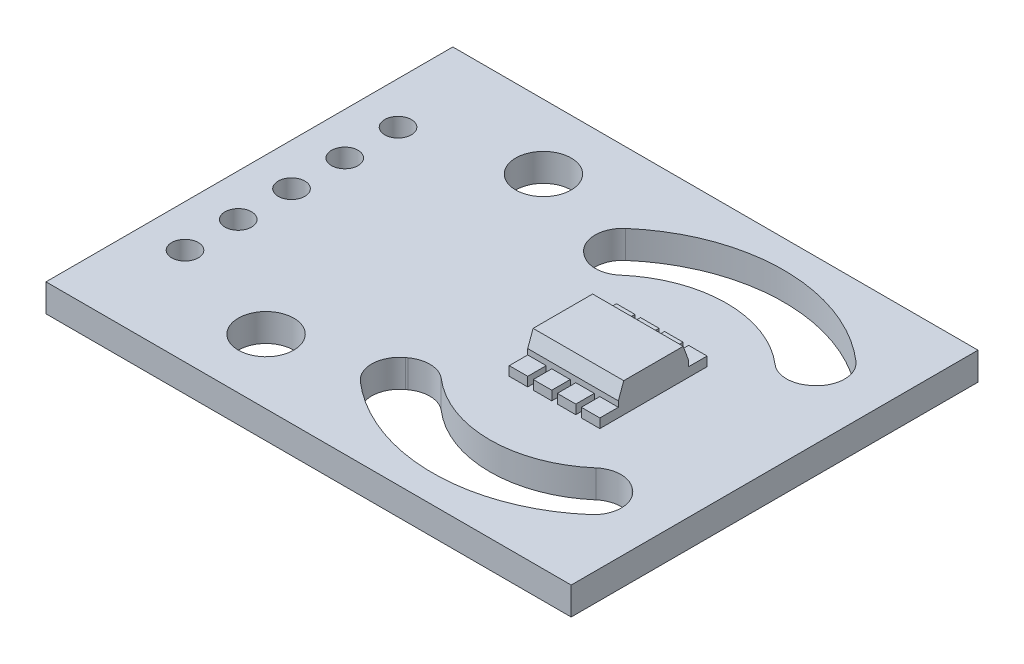
SolidWorks part; units mm, degrees
ref_plane "Спереди" through (0, 0, 0) normal (0, 0, 1) x (1, 0, 0)
ref_plane "Сверху" through (0, 0, 0) normal (0, 1, 0) x (1, 0, 0)
ref_plane "Справа" through (0, 0, 0) normal (1, 0, 0) x (0, 0, -1)
sketch "Sketch1" plane through (0, 0, 0) normal (0, 1, 0) x (1, 0, 0)
  line L1 (14.2, -11) -> (-14.2, -11)
  line L2 (14.2, -11) -> (14.2, 11)
  line L3 (14.2, 11) -> (-14.2, 11)
  line L4 (-14.2, -11) -> (-14.2, 11)
  line L5 (14.2, -11) -> (-14.2, 11) construction
  line L6 (14.2, 11) -> (-14.2, -11) construction
  point P0 (0, 0)
  dimension "D1" = 22
  dimension "D2" = 28.4
extrude "Boss-Extrude1" add sketch "Sketch1" along normal blind 1.5
sketch "Sketch2" plane through (0, 1.5, 0) normal (0, 1, 0) x (1, 0, 0)
  line L0 (-14.2, 0) -> (14.2, 0) construction
  line L1 (-14.2, 11) -> (-14.2, -11) construction
  line L2 (14.2, -11) -> (14.2, 11) construction
  line L3 (-2.3, 11) -> (-2.3, -11) construction
  line L4 (14.2, 11) -> (-14.2, 11) construction
  line L5 (-14.2, -11) -> (14.2, -11) construction
  line L6 (12.7, -11) -> (12.7, 11) construction
  line L7 (12.7, 11) -> (-2.3, -11) construction
  line L8 (0.2, 11) -> (0.2, -11) construction
  line L9 (10.2, -11) -> (10.2, 11) construction
  line L10 (0.2, 11) -> (10.2, -11) construction
  line L11 (-2.3, 5.831) -> (0.2, 3.995)
  line L12 (10.2, 3.995) -> (12.7, 5.831)
  line L13 (10.2, -3.995) -> (12.7, -5.831)
  line L14 (-2.3, -5.831) -> (0.2, -3.995)
  line L15 (-5.8, 11) -> (-5.8, -11) construction
  line L16 (-11.9229, 5.76) -> (-11.9229, -5.76) construction
  line L18 (-11.2029, -6) -> (-12.6029, -6) construction
  line L19 (-11.2029, -6) -> (-11.2029, 6) construction
  line L20 (-11.2029, 6) -> (-12.6029, 6) construction
  line L21 (-12.6029, -6) -> (-12.6029, 6) construction
  line L22 (-11.2029, -6) -> (-12.6029, 6) construction
  line L23 (-11.2029, 6) -> (-12.6029, -6) construction
  circle A0 centre (5.2, 0) radius 9.5 construction
  circle A1 centre (5.2, 0) radius 6.4 construction
  arc A2 (-2.3, 5.831) -> (12.7, 5.831) centre (5.2, 0) cw
  arc A3 (0.2, 3.995) -> (10.2, 3.995) centre (5.2, 0) cw
  arc A4 (0.2, -3.995) -> (10.2, -3.995) centre (5.2, 0) ccw
  arc A5 (-2.3, -5.831) -> (12.7, -5.831) centre (5.2, 0) ccw
  circle A6 centre (-5.8, 7.5) radius 1.5
  circle A7 centre (-5.8, -7.5) radius 1.5
  circle A8 centre (-11.9229, 5.76) radius 0.72
  circle A9 centre (-11.9229, 2.88) radius 0.72
  circle A10 centre (-11.9229, 0) radius 0.72
  circle A11 centre (-11.9229, -2.88) radius 0.72
  circle A12 centre (-11.9229, -5.76) radius 0.72
  point P21 (0.2, 3.995)
  point P22 (-2.3, 5.831)
  point P23 (10.5517, 7.8492)
  point P24 (10.2, 3.995)
  point P25 (10.2, -3.995)
  point P26 (10.2, -8.0777)
  point P27 (0.2, -8.0777)
  point P28 (0.2, -3.995)
  point P29 (-2.3, -5.831)
  point P30 (12.7, 5.831)
  point P31 (12.7, -5.831)
  point P32 (10.2, -8.0777)
  point P51 (0, 0)
  point P52 (0, 0)
  point P53 (0, 0)
  point P54 (-11.9029, 0)
  point P69 (0, 0)
  point P70 (0, 0)
  point P71 (0, 0)
  point P72 (0, 0)
  point P73 (-11.6189, -2.7806)
  dimension "D2" = 19
  dimension "D3" = 12.8
  dimension "D6" = 3
  dimension "D16" = 1.44
  dimension "D1" = 9
  dimension "D4" = 15
  dimension "D5" = 10
  dimension "D7" = 20
  dimension "D8" = 15
  dimension "D9" = 7.5
  dimension "D10" = 2.88
  dimension "D11" = 12
  dimension "D12" = 1.4
  dimension "D13" = 2.88
  dimension "D14" = 2.88
  dimension "D15" = 2.88
  dimension "D17" = 11
extrude "Cut-Extrude1" cut sketch "Sketch2" against normal through all
fillet "Fillet1" radius 1.5 8 edges at (12.7, 0.75, 5.831) (10.2, 0.75, 3.995) (0.2, 0.75, 3.995) (-2.3, 0.75, 5.831) (10.2, 0.75, -3.995) (12.7, 0.75, -5.831) (0.2, 0.75, -3.995) (-2.3, 0.75, -5.831)
sketch "Sketch3" plane through (0, 1.5, 0) normal (0, 1, 0) x (1, 0, 0)
  line L0 (5.2, 6.4) -> (5.2, -6.4) construction
  line L2 (7.65, -1.9) -> (2.75, -1.9)
  line L3 (7.65, -1.9) -> (7.65, 1.9)
  line L4 (7.65, 1.9) -> (2.75, 1.9)
  line L5 (2.75, -1.9) -> (2.75, 1.9)
  line L6 (7.65, -1.9) -> (2.75, 1.9) construction
  line L7 (7.65, 1.9) -> (2.75, -1.9) construction
  arc A0 (9.3845, 4.8425) -> (1.0155, 4.8425) centre (5.2, 0) ccw construction
  arc A1 (1.0155, -4.8425) -> (9.3845, -4.8425) centre (5.2, 0) ccw construction
  point P8 (5.2, 0)
  dimension "D1" = 3.8
  dimension "D2" = 4.9
extrude "Boss-Extrude2" add sketch "Sketch3" along normal blind 1.6
chamfer "Chamfer1" distance 0.8 angle 20 2 edges at (5.2, 3.1, 1.9) (5.2, 3.1, -1.9)
sketch "Sketch6" plane through (0, 1.5, 0) normal (0, 1, 0) x (1, 0, 0)
  line L0 (2.75, -1.9) -> (2.75, -2.9)
  line L1 (2.75, -2.9) -> (3.75, -2.9)
  line L2 (3.75, -2.9) -> (3.75, -1.9)
  line L3 (2.75, -1.9) -> (7.65, -1.9) construction
  line L4 (3.75, -1.9) -> (2.75, -1.9)
  line L5 (2.75, 1.9) -> (2.75, 2.9)
  line L6 (2.75, 2.9) -> (3.75, 2.9)
  line L7 (3.75, 2.9) -> (3.75, 1.9)
  line L8 (7.65, 1.9) -> (2.75, 1.9) construction
  line L9 (3.75, 1.9) -> (2.75, 1.9)
  line L10 (5.05, -2.9) -> (5.05, -1.9)
  line L11 (4.05, -1.9) -> (4.05, -2.9)
  line L12 (4.05, -2.9) -> (5.05, -2.9)
  line L13 (5.05, -1.9) -> (4.05, -1.9)
  line L14 (5.05, 2.9) -> (5.05, 1.9)
  line L15 (4.05, 2.9) -> (5.05, 2.9)
  line L16 (4.05, 1.9) -> (4.05, 2.9)
  line L17 (5.05, 1.9) -> (4.05, 1.9)
  line L18 (6.35, -2.9) -> (6.35, -1.9)
  line L19 (5.35, -1.9) -> (5.35, -2.9)
  line L20 (5.35, -2.9) -> (6.35, -2.9)
  line L21 (6.35, -1.9) -> (5.35, -1.9)
  line L22 (6.35, 2.9) -> (6.35, 1.9)
  line L23 (5.35, 2.9) -> (6.35, 2.9)
  line L24 (5.35, 1.9) -> (5.35, 2.9)
  line L25 (6.35, 1.9) -> (5.35, 1.9)
  line L26 (7.65, -2.9) -> (7.65, -1.9)
  line L27 (6.65, -1.9) -> (6.65, -2.9)
  line L28 (6.65, -2.9) -> (7.65, -2.9)
  line L29 (7.65, -1.9) -> (6.65, -1.9)
  line L30 (7.65, 2.9) -> (7.65, 1.9)
  line L31 (6.65, 2.9) -> (7.65, 2.9)
  line L32 (6.65, 1.9) -> (6.65, 2.9)
  line L33 (7.65, 1.9) -> (6.65, 1.9)
  dimension "D1" = 1
  dimension "D2" = 1
  dimension "D3" = 4
extrude "Boss-Extrude3" add sketch "Sketch6" along normal blind 0.5
